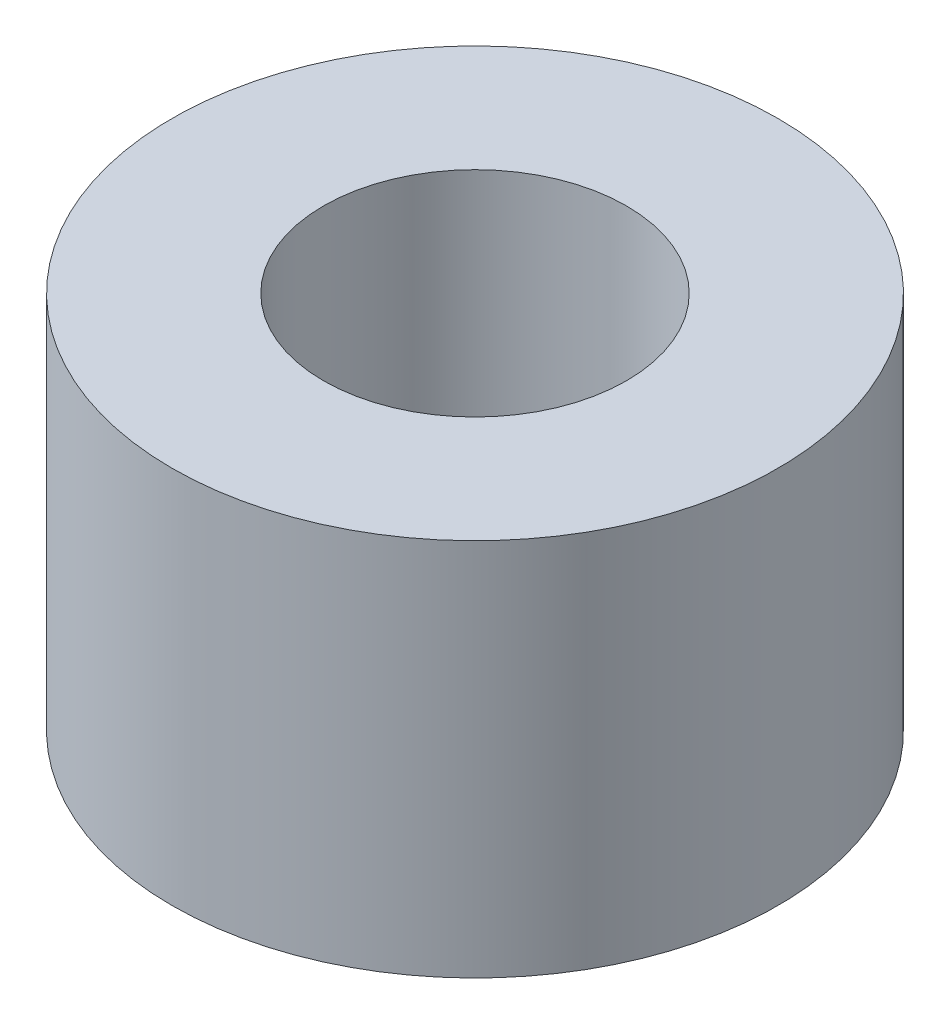
SolidWorks part; units mm, degrees
ref_plane "前视基准面" through (0, 0, 0) normal (0, 0, 1) x (1, 0, 0)
ref_plane "上视基准面" through (0, 0, 0) normal (0, 1, 0) x (1, 0, 0)
ref_plane "右视基准面" through (0, 0, 0) normal (1, 0, 0) x (0, 0, -1)
sketch "草图1" plane through (0, 0, 0) normal (0, 1, 0) x (1, 0, 0)
  circle A0 centre (0, 0) radius 4
  circle A1 centre (0, 0) radius 2
extrude "凸台-拉伸1" add sketch "草图1" along normal blind 5
sketch "草图2" plane through (0, 5, 0) normal (0, 1, 0) x (1, 0, 0)
  circle A0 centre (0, 0) radius 2
sketch "草图3" plane through (0, 0, 0) normal (0, -1, 0) x (1, 0, 0)
  circle A0 centre (0, 0) radius 2
